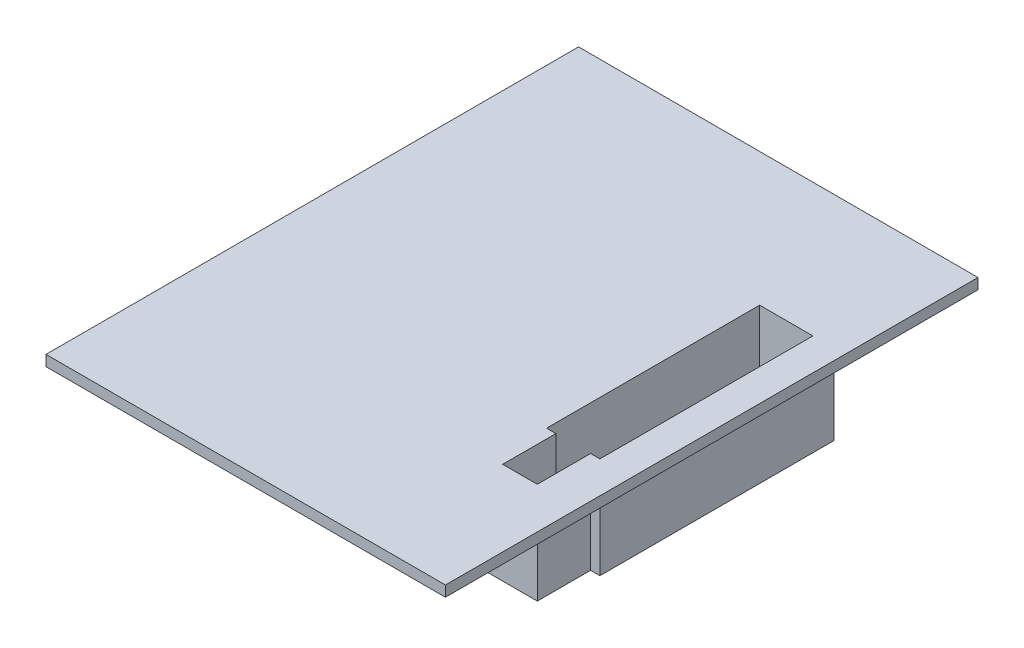
SolidWorks part; units mm, degrees
ref_plane "Front Plane" through (0, 0, 0) normal (0, 0, 1) x (1, 0, 0)
ref_plane "Top Plane" through (0, 0, 0) normal (0, 1, 0) x (1, 0, 0)
ref_plane "Right Plane" through (0, 0, 0) normal (1, 0, 0) x (0, 0, -1)
sketch "Sketch1" plane through (0, 0, 0) normal (0, 1, 0) x (1, 0, 0)
  line L1 (-37.5, -50) -> (37.5, -50)
  line L2 (-37.5, -50) -> (-37.5, 50)
  line L3 (-37.5, 50) -> (37.5, 50)
  line L4 (37.5, -50) -> (37.5, 50)
  line L5 (-37.5, -50) -> (37.5, 50) construction
  line L6 (-37.5, 50) -> (37.5, -50) construction
  point P0 (0, 0)
  dimension "D1" = 75
  dimension "D2" = 100
extrude "Boss-Extrude1" add sketch "Sketch1" along normal blind 2
sketch "Sketch2" plane through (0, 2, 0) normal (0, 1, 0) x (1, 0, 0)
  line L0 (37.5, -50) -> (37.5, 50) construction
  line L1 (21.5, 25) -> (31.5, 25)
  line L2 (21.5, 25) -> (21.5, -25)
  line L3 (21.5, -25) -> (31.5, -25)
  line L4 (31.5, 25) -> (31.5, -25)
  point P6 (31.5, 0)
  dimension "D1" = 10
  dimension "D2" = 6
  dimension "D3" = 50
extrude "Cut-Extrude1" cut sketch "Sketch2" against normal up to next
sketch "Sketch3" plane through (0, 0, 0) normal (0, -1, 0) x (1, 0, 0)
  line L0 (26.5, 25) -> (26.5, -25) construction
  line L1 (21.5, 25) -> (23.25, 25)
  line L2 (21.5, 25) -> (21.5, 15)
  line L3 (21.5, 15) -> (23.25, 15)
  line L4 (23.25, 25) -> (23.25, 15)
  line L5 (21.5, 25) -> (31.5, 25) construction
  line L6 (31.5, -25) -> (21.5, -25) construction
  line L7 (29.75, 25) -> (29.75, 15)
  line L8 (31.5, 15) -> (29.75, 15)
  line L9 (31.5, 25) -> (31.5, 15)
  line L10 (31.5, 25) -> (29.75, 25)
  dimension "D1" = 6.5
  dimension "D2" = 10
extrude "Boss-Extrude2" add sketch "Sketch3" against normal up to vertex (2 mm away)
sketch "Sketch4" plane through (0, 0, 0) normal (0, -1, 0) x (1, 0, 0)
  line L21 (33.5, 17) -> (31.75, 17)
  line L22 (33.5, -27) -> (33.5, 17)
  line L23 (19.5, -27) -> (33.5, -27)
  line L24 (19.5, 17) -> (19.5, -27)
  line L25 (21.25, 17) -> (19.5, 17)
  line L26 (21.25, 27) -> (21.25, 17)
  line L27 (31.75, 27) -> (21.25, 27)
  line L28 (31.75, 17) -> (31.75, 27)
  line L29 (33.5, 17) -> (31.75, 17)
  line L30 (33.5, -27) -> (33.5, 17)
  line L31 (19.5, -27) -> (33.5, -27)
  line L32 (19.5, 17) -> (19.5, -27)
  line L33 (21.25, 17) -> (19.5, 17)
  line L34 (21.25, 27) -> (21.25, 17)
  line L35 (31.75, 27) -> (21.25, 27)
  line L36 (31.75, 17) -> (31.75, 27)
  line L45 (31.5, 15) -> (29.75, 15)
  line L46 (31.5, -25) -> (31.5, 15)
  line L47 (21.5, -25) -> (31.5, -25)
  line L48 (21.5, 15) -> (21.5, -25)
  line L49 (23.25, 15) -> (21.5, 15)
  line L50 (23.25, 25) -> (23.25, 15)
  line L51 (29.75, 25) -> (23.25, 25)
  line L52 (29.75, 15) -> (29.75, 25)
  line L53 (31.5, 15) -> (29.75, 15)
  line L54 (31.5, -25) -> (31.5, 15)
  line L55 (21.5, -25) -> (31.5, -25)
  line L56 (21.5, 15) -> (21.5, -25)
  line L57 (23.25, 15) -> (21.5, 15)
  line L58 (23.25, 25) -> (23.25, 15)
  line L59 (29.75, 25) -> (23.25, 25)
  line L60 (29.75, 15) -> (29.75, 25)
  dimension "D1" = 2
  dimension "D2" = 0
extrude "Boss-Extrude3" add sketch "Sketch4" along normal blind 15
ref_plane "Plane1" through (26.5, 0, 0) normal (-1, 0, 0) x (0, 0, 1)
sketch "Sketch5" plane through (26.5, 0, 0) normal (-1, 0, 0) x (0, 0, 1)
  line L0 (-50, 2) -> (50, 2) construction
  line L1 (27, -15) -> (17, -15) construction
  circle A0 centre (22, -3.5) radius 1.75
  point P6 (0, 0)
  point P7 (22, -15)
  dimension "D1" = 3.5
  dimension "D2" = 5.5
extrude "Cut-Extrude2" cut sketch "Sketch5" against normal through all both and the other way through all
